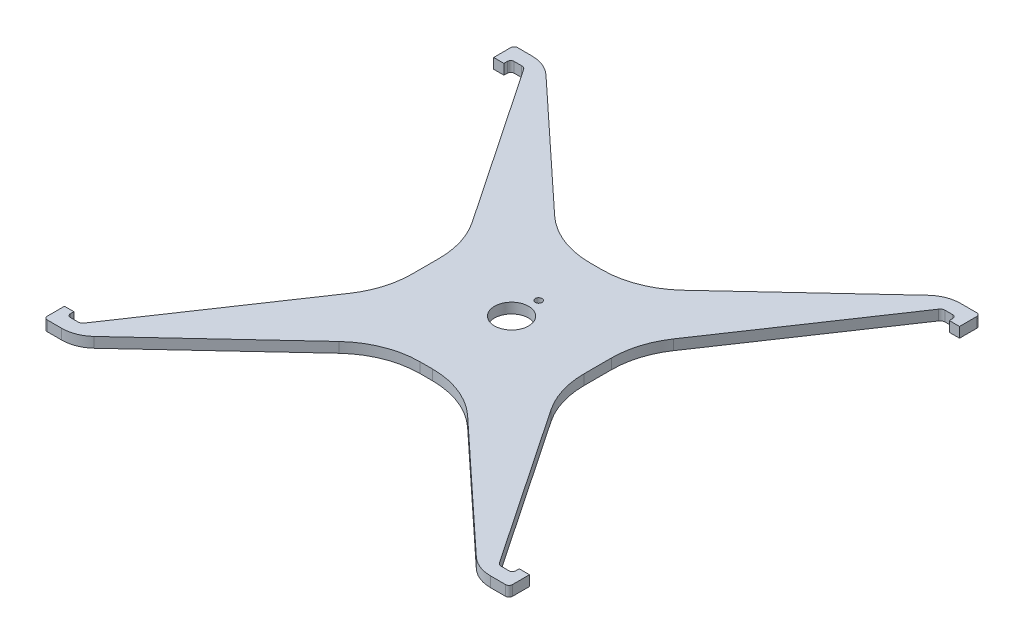
SolidWorks part; units mm, degrees
material "ABS"
ref_plane "Front Plane" through (0, 0, 0) normal (0, 0, 1) x (1, 0, 0)
ref_plane "Top Plane" through (0, 0, 0) normal (0, 1, 0) x (1, 0, 0)
ref_plane "Right Plane" through (0, 0, 0) normal (1, 0, 0) x (0, 0, -1)
sketch "Sketch1" plane through (0, 0, 0) normal (0, 1, 0) x (1, 0, 0)
  line L0 (-65.25, 63) -> (-68.25, 63)
  line L1 (0, 0) -> (0, 7.92)
  line L2 (-68.25, 63) -> (-68.25, 68)
  line L3 (-67.25, 69) -> (-63.0587, 69)
  line L4 (-64.25, 65) -> (-62.0476, 65)
  line L5 (-60.804, 64.3388) -> (-29.5241, 17.9644)
  line L6 (-56.2432, 66.3178) -> (-19.0798, 31.7055)
  line L7 (-68, -63) -> (-68, -68)
  line L8 (-65.25, -64) -> (-65.25, -63)
  line L9 (-65.25, -63) -> (-68, -63)
  line L10 (-55.9932, -66.3178) -> (-18.8298, -31.7055)
  line L11 (1.7912, -25) -> (-1.7912, -25)
  line L12 (25.25, -3.9845) -> (25.25, 3.9845)
  line L13 (1.5412, 25) -> (-2.0412, 25)
  line L14 (-25.25, -3.9845) -> (-25.25, 3.9845)
  line L15 (65.25, 63) -> (65.25, 64)
  line L16 (-65.25, 63) -> (-65.25, 64)
  line L17 (-60.804, -64.3388) -> (-29.5241, -17.9644)
  line L18 (-64.25, -65) -> (-62.0476, -65)
  line L19 (-67, -69) -> (-62.8087, -69)
  line L20 (67.25, -69) -> (62.8087, -69)
  line L22 (64.25, -65) -> (62.0476, -65)
  line L23 (60.804, -64.3388) -> (29.5241, -17.9644)
  line L24 (55.9932, -66.3178) -> (18.8298, -31.7055)
  line L25 (65.25, -63) -> (68.25, -63)
  line L26 (65.25, -64) -> (65.25, -63)
  line L27 (68.25, -63) -> (68.25, -68)
  line L28 (55.7432, 66.3178) -> (18.5798, 31.7055)
  line L29 (60.804, 64.3388) -> (29.5241, 17.9644)
  line L30 (64.25, 65) -> (62.0476, 65)
  line L31 (67.25, 69) -> (62.5587, 69)
  line L32 (68.25, 63) -> (68.25, 68)
  line L34 (65.25, 63) -> (68.25, 63)
  circle A0 centre (0, 0) radius 5
  arc A1 (-55.9932, -66.3178) -> (-62.8087, -69) centre (-62.8087, -59) cw
  arc A2 (62.8087, -69) -> (55.9932, -66.3178) centre (62.8087, -59) cw
  arc A3 (55.7432, 66.3178) -> (62.5587, 69) centre (62.5587, 59) cw
  arc A4 (-63.0587, 69) -> (-56.2432, 66.3178) centre (-63.0587, 59) cw
  arc A5 (-18.8298, -31.7055) -> (-1.7912, -25) centre (-1.7912, -50) cw
  arc A6 (18.8298, -31.7055) -> (1.7912, -25) centre (1.7912, -50) ccw
  arc A7 (29.5241, -17.9644) -> (25.25, -3.9845) centre (50.25, -3.9845) cw
  arc A8 (29.5241, 17.9644) -> (25.25, 3.9845) centre (50.25, 3.9845) ccw
  arc A9 (-29.5241, 17.9644) -> (-25.25, 3.9845) centre (-50.25, 3.9845) cw
  arc A10 (-29.5241, -17.9644) -> (-25.25, -3.9845) centre (-50.25, -3.9845) ccw
  arc A11 (18.5798, 31.7055) -> (1.5412, 25) centre (1.5412, 50) cw
  arc A12 (-19.0798, 31.7055) -> (-2.0412, 25) centre (-2.0412, 50) ccw
  circle A13 centre (0, 7.92) radius 1
  arc A14 (-62.0476, 65) -> (-60.804, 64.3388) centre (-62.0476, 63.5) cw
  arc A15 (-60.804, -64.3388) -> (-62.0476, -65) centre (-62.0476, -63.5) cw
  arc A16 (62.0476, -65) -> (60.804, -64.3388) centre (62.0476, -63.5) cw
  arc A17 (60.804, 64.3388) -> (62.0476, 65) centre (62.0476, 63.5) cw
  arc A18 (-64.25, -65) -> (-65.25, -64) centre (-64.25, -64) cw
  arc A19 (-68, -68) -> (-67, -69) centre (-67, -68) ccw
  arc A20 (67.25, -69) -> (68.25, -68) centre (67.25, -68) ccw
  arc A21 (64.25, -65) -> (65.25, -64) centre (64.25, -64) ccw
  arc A22 (67.25, 69) -> (68.25, 68) centre (67.25, 68) cw
  arc A23 (65.25, 64) -> (64.25, 65) centre (64.25, 64) ccw
  arc A24 (-65.25, 64) -> (-64.25, 65) centre (-64.25, 64) cw
  arc A25 (-68.25, 68) -> (-67.25, 69) centre (-67.25, 68) cw
  point P25 (-11.88, 25)
  point P49 (-58.8732, -69)
  point P52 (58.8732, -69)
  point P55 (58.6232, 69)
  point P58 (-59.1232, 69)
  point P64 (-11.88, 25)
  point P69 (-61.25, 65)
  point P78 (-65.25, -65)
  point P91 (-65.25, 65)
  point P94 (-68.25, 69)
  dimension "D6" = 25
  dimension "D12" = 10
  dimension "D7" = 65.25
  dimension "D13" = 1.5
  dimension "D14" = 1
  dimension "D1" = 65.25
  dimension "D2" = 65
  dimension "D3" = 65
  dimension "D4" = 2
  dimension "D5" = 3
  dimension "D8" = 4
  dimension "D9" = 3
  dimension "D10" = 6
  dimension "D11" = 124
extrude "Boss-Extrude1" add sketch "Sketch1" along normal blind 3
